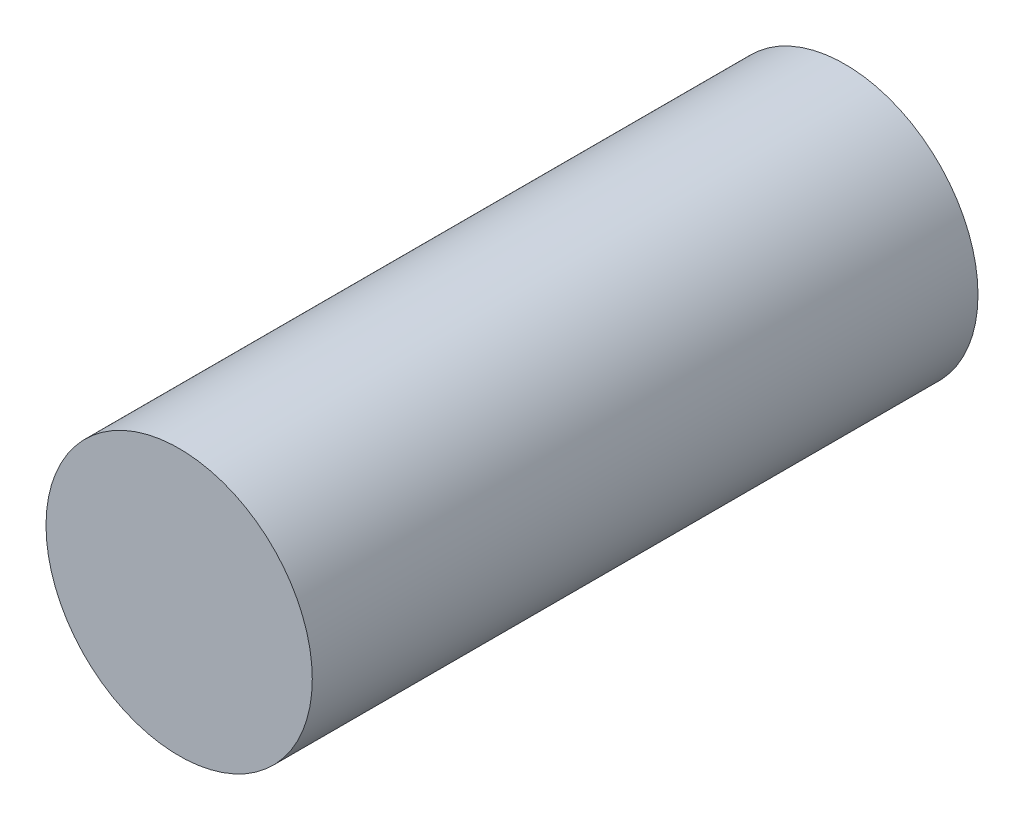
SolidWorks part; units mm, degrees
ref_plane "Front Plane" through (0, 0, 0) normal (0, 0, 1) x (1, 0, 0)
ref_plane "Top Plane" through (0, 0, 0) normal (0, 1, 0) x (1, 0, 0)
ref_plane "Right Plane" through (0, 0, 0) normal (1, 0, 0) x (0, 0, -1)
other "Configuration Table"
sketch "草图1" plane through (0, 0, 0) normal (0, 0, 1) x (1, 0, 0)
  circle A0 centre (-3.4106, 2.3573) radius 3
  dimension "D1" = 6
extrude "凸台-拉伸1" add sketch "草图1" along normal blind 15
